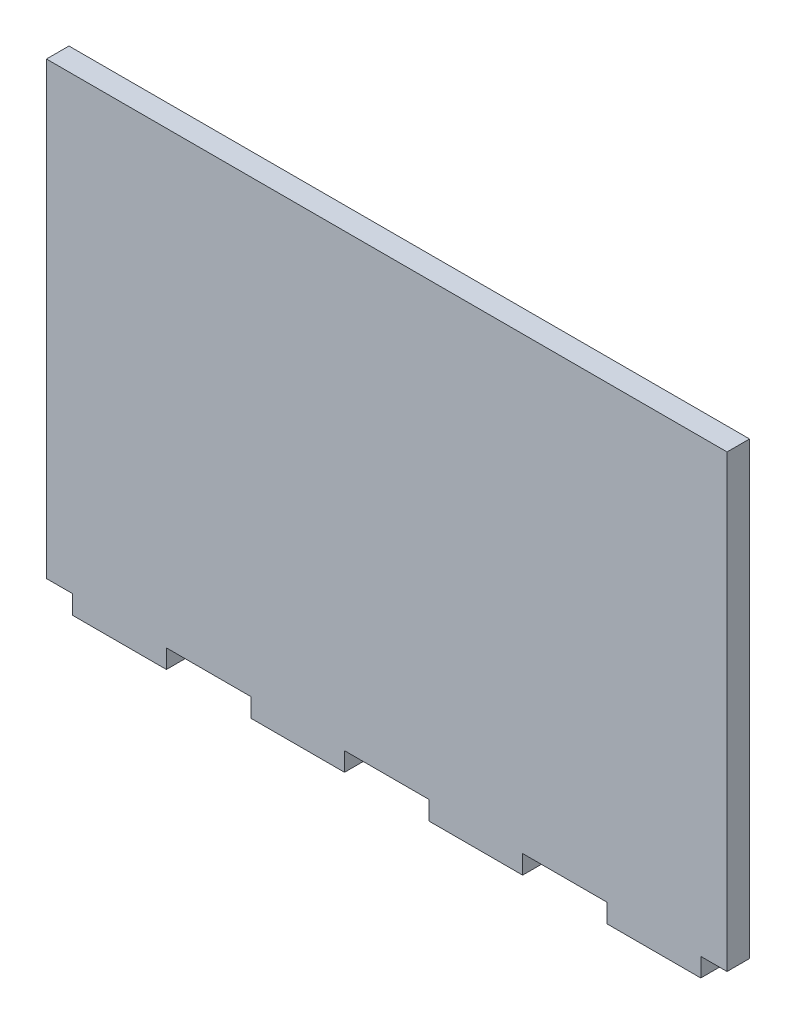
SolidWorks part; units mm, degrees
ref_plane "Plan de face" through (0, 0, 0) normal (0, 0, 1) x (1, 0, 0)
ref_plane "Plan de dessus" through (0, 0, 0) normal (0, 1, 0) x (1, 0, 0)
ref_plane "Plan de droite" through (0, 0, 0) normal (1, 0, 0) x (0, 0, -1)
sketch "Esquisse1" plane through (0, 0, 0) normal (0, 0, 1) x (1, 0, 0)
  line L1 (-117.0401, 98.2674) -> (64.4599, 98.2674)
  line L2 (-117.0401, 98.2674) -> (-117.0401, -21.7326)
  line L3 (-117.0401, -21.7326) -> (64.4599, -21.7326)
  line L4 (64.4599, 98.2674) -> (64.4599, -21.7326)
  line L5 (-110.0301, -21.7326) -> (-85.0501, -21.7326)
  line L6 (-110.0301, -21.7326) -> (-110.0301, -26.7326)
  line L7 (-110.0301, -26.7326) -> (-85.0501, -26.7326)
  line L8 (-85.0501, -21.7326) -> (-85.0501, -26.7326)
  line L9 (-62.5301, -21.7326) -> (-37.5501, -21.7326)
  line L10 (-62.5301, -21.7326) -> (-62.5301, -26.7326)
  line L11 (-62.5301, -26.7326) -> (-37.5501, -26.7326)
  line L12 (-37.5501, -21.7326) -> (-37.5501, -26.7326)
  line L13 (-15.0301, -21.7326) -> (9.9499, -21.7326)
  line L14 (-15.0301, -21.7326) -> (-15.0301, -26.7326)
  line L15 (-15.0301, -26.7326) -> (9.9499, -26.7326)
  line L16 (9.9499, -21.7326) -> (9.9499, -26.7326)
  line L17 (32.4699, -21.7326) -> (57.4499, -21.7326)
  line L18 (32.4699, -21.7326) -> (32.4699, -26.7326)
  line L19 (32.4699, -26.7326) -> (57.4499, -26.7326)
  line L20 (57.4499, -21.7326) -> (57.4499, -26.7326)
  dimension "D1" = 24.98
  dimension "D2" = 24.98
  dimension "D3" = 24.98
  dimension "D4" = 24.98
  dimension "D5" = 22.52
  dimension "D6" = 22.52
  dimension "D7" = 22.52
  dimension "D8" = 7.01
  dimension "D9" = 120
  dimension "D10" = 181.5
  dimension "D11" = 5
extrude "Boss.-Extru.1" add sketch "Esquisse1" along normal blind 6 contours L4 L1 L2 L3 | L8 L3 L6 L7 | L12 L3 L10 L11 | L16 L3 L14 L15 | L20 L3 L18 L19
